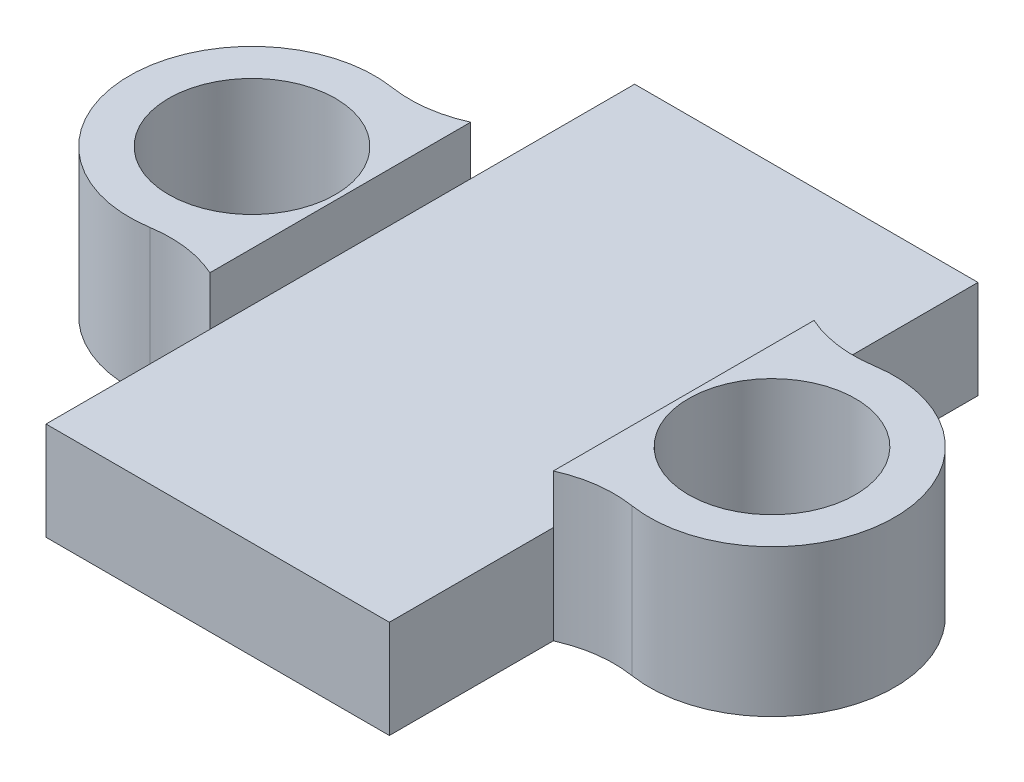
SolidWorks part; units mm, degrees
ref_plane "Alzado" through (0, 0, 0) normal (0, 0, 1) x (1, 0, 0)
ref_plane "Planta" through (0, 0, 0) normal (0, 1, 0) x (1, 0, 0)
ref_plane "Vista lateral" through (0, 0, 0) normal (1, 0, 0) x (0, 0, -1)
sketch "Croquis1" plane through (0, 0, 0) normal (0, 1, 0) x (1, 0, 0)
  line L0 (0, -16.4018) -> (0, 78.9163) construction
  line L1 (-63.9099, 0) -> (63.9099, 0) construction
  line L2 (-3.5, 6) -> (3.5, 6)
  line L3 (3.5, 6) -> (3.5, 2.6575)
  line L4 (-3.5, -6) -> (3.5, -6)
  line L5 (3.5, -6) -> (3.5, -2.6575)
  line L6 (-3.5, -6) -> (-3.5, -2.6575)
  line L7 (-3.5, 6) -> (-3.5, 2.6575)
  circle A0 centre (5.3, 0) radius 1.7
  arc A1 (4.911, -2.4695) -> (4.911, 2.4695) centre (5.3, 0) ccw
  arc A2 (3.5, 2.6575) -> (4.911, 2.4695) centre (4.5219, 4.9391) ccw
  arc A3 (3.5, -2.6575) -> (4.911, -2.4695) centre (4.5219, -4.9391) cw
  arc A4 (-3.5, -2.6575) -> (-4.911, -2.4695) centre (-4.5219, -4.9391) ccw
  arc A5 (-3.5, 2.6575) -> (-4.911, 2.4695) centre (-4.5219, 4.9391) cw
  arc A6 (-4.911, -2.4695) -> (-4.911, 2.4695) centre (-5.3, 0) cw
  circle A7 centre (-5.3, 0) radius 1.7
  point P6 (-7.8, 0)
  point P10 (7.8, 0)
  point P19 (0, 0)
  point P28 (0, -6)
  point P29 (-7.8, 0)
  point P30 (0, 6)
  point P31 (7.8, 0)
  dimension "D1" = 3.4
  dimension "D5" = 5
  dimension "D6" = 5
  dimension "D2" = 7.8
  dimension "D3" = 7.8
  dimension "D4" = 6
  dimension "D7" = 7
extrude "Saliente-Extruir1" add sketch "Croquis1" along normal blind 2
sketch "Croquis5" plane through (0, 2, 0) normal (0, 1, 0) x (1, 0, 0)
  line L0 (3.5, 2.6575) -> (3.5, -2.6575)
  line L1 (-3.5, -6) -> (3.5, -6) construction
  line L2 (3.5, 6) -> (-3.5, 6) construction
  line L3 (-3.5, -2.6575) -> (-3.5, 2.6575)
  line L7 (3.4556, 6) -> (3.5, 6)
  line L8 (3.5, -6) -> (3.5, -2.6575)
  line L9 (-3.5, -6) -> (3.5, -6)
  line L10 (3.5, -6) -> (3.5, -2.6575)
  line L11 (-3.5, -6) -> (3.5, -6) construction
  line L12 (3.5, 2.6575) -> (3.5, 6)
  line L13 (3.5, 2.6575) -> (3.5, 6)
  line L14 (3.4556, -6) -> (3.5, -6)
  arc A0 (-3.5, 2.6575) -> (-4.911, 2.4695) centre (-4.5219, 4.9391) cw
  arc A1 (-3.5, -2.6575) -> (-4.911, -2.4695) centre (-4.5219, -4.9391) ccw
  arc A2 (-4.911, -2.4695) -> (-4.911, 2.4695) centre (-5.3, 0) cw
  circle A3 centre (-5.3, 0) radius 1.7
  arc A12 (3.5, 2.6575) -> (4.911, 2.4695) centre (4.5219, 4.9391) ccw
  arc A13 (4.911, -2.4695) -> (4.911, 2.4695) centre (5.3, 0) ccw
  arc A14 (4.911, -2.4695) -> (3.5, -2.6575) centre (4.5219, -4.9391) ccw
  arc A15 (3.5, 2.6575) -> (4.911, 2.4695) centre (4.5219, 4.9391) ccw
  arc A16 (4.911, -2.4695) -> (4.911, 2.4695) centre (5.3, 0) ccw
  arc A17 (4.911, -2.4695) -> (3.5, -2.6575) centre (4.5219, -4.9391) ccw
  circle A18 centre (5.3, 0) radius 1.7
  dimension "D2" = 0
  dimension "D3" = 0
extrude "Boss-Extrude1" add sketch "Croquis5" along normal blind 1
